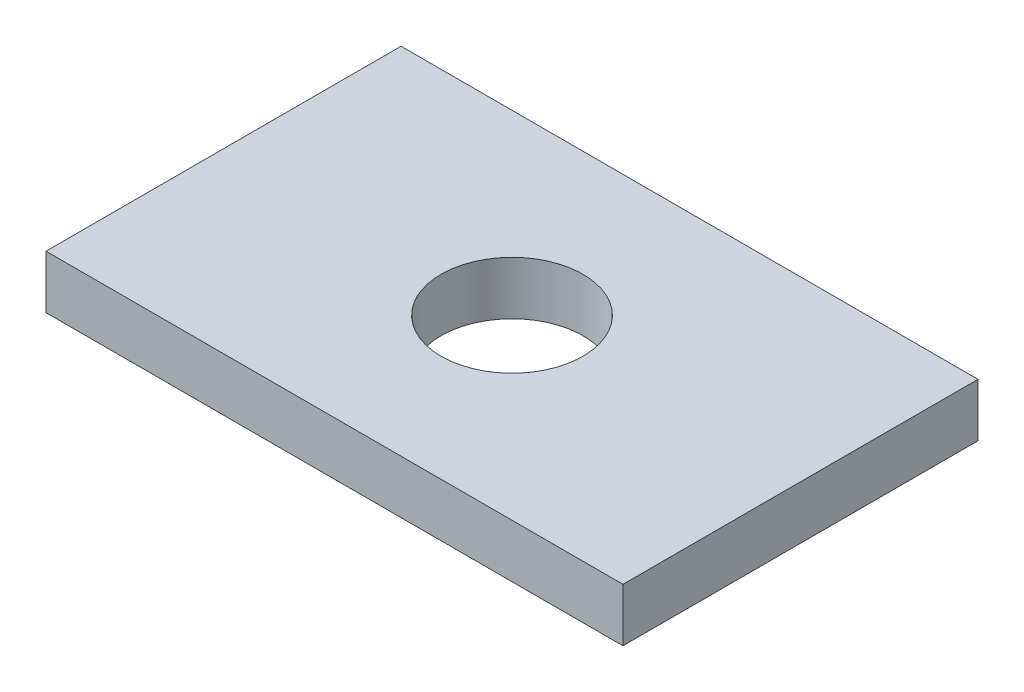
SolidWorks part; units mm, degrees
ref_plane "Front Plane" through (0, 0, 0) normal (0, 0, 1) x (1, 0, 0)
ref_plane "Top Plane" through (0, 0, 0) normal (0, 1, 0) x (1, 0, 0)
ref_plane "Right Plane" through (0, 0, 0) normal (1, 0, 0) x (0, 0, -1)
sketch "Sketch1" plane through (0, 0, 0) normal (0, 0, 1) x (1, 0, 0)
  line L1 (-32.5, -3) -> (32.5, -3)
  line L2 (-32.5, -3) -> (-32.5, 3)
  line L3 (-32.5, 3) -> (32.5, 3)
  line L4 (32.5, -3) -> (32.5, 3)
  line L5 (-32.5, -3) -> (32.5, 3) construction
  line L6 (-32.5, 3) -> (32.5, -3) construction
  point P0 (0, 0)
  dimension "D1" = 6
  dimension "D2" = 65
extrude "Boss-Extrude1" add sketch "Sketch1" along normal blind 40
sketch "Sketch2" plane through (0, 3, 0) normal (0, 1, 0) x (1, 0, 0)
  line L0 (-32.5, 0) -> (32.5, -40) construction
  line L1 (-32.5, -40) -> (32.5, 0) construction
  circle A0 centre (0, -20) radius 8
  point P11 (0, -20)
  dimension "D1" = 16
extrude "Cut-Extrude1" cut sketch "Sketch2" against normal through all
ref_plane "Plane1" through (0, 0, 20) normal (0, 0, 1) x (1, 0, 0)
ref_plane "Plane2" through (-10, 0, 10) normal (0.7071, 0, -0.7071) x (-0.7071, 0, -0.7071)
ref_plane "Plane3" through (10, 0, 10) normal (0.7071, 0, 0.7071) x (0.7071, 0, -0.7071)
